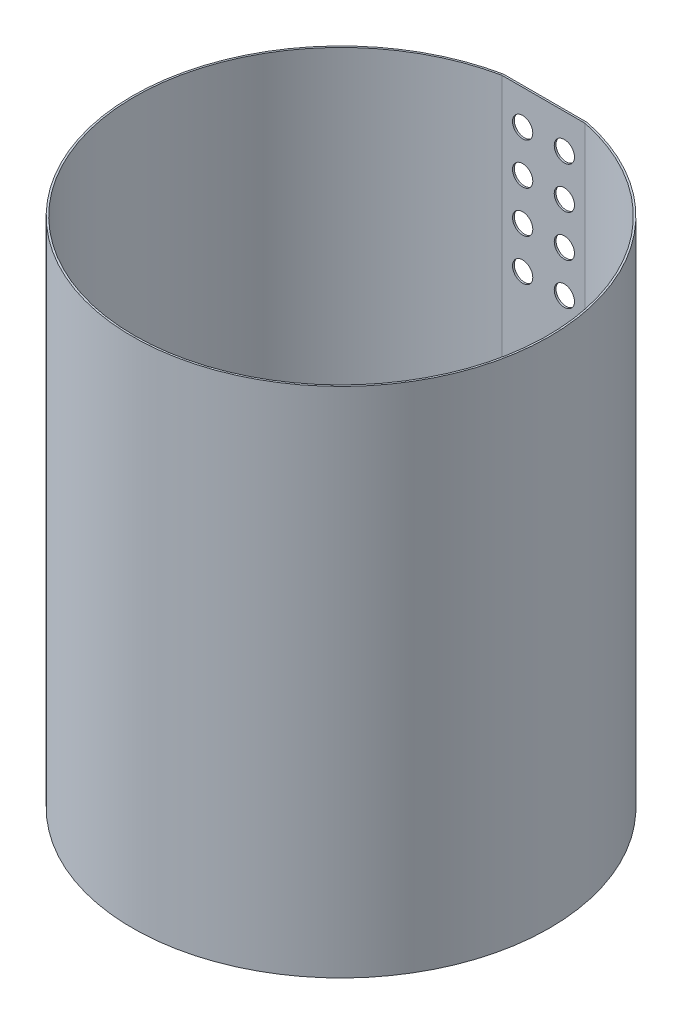
SolidWorks part; units mm, degrees
material "AISI 316 Stainless Steel Sheet (SS)"
ref_plane "Front Plane" through (0, 0, 0) normal (0, 0, 1) x (1, 0, 0)
ref_plane "Top Plane" through (0, 0, 0) normal (0, 1, 0) x (1, 0, 0)
ref_plane "Right Plane" through (0, 0, 0) normal (1, 0, 0) x (0, 0, -1)
sketch "Sketch1" plane through (0, 0, 0) normal (0, 1, 0) x (1, 0, 0)
  line L0 (-35, 169.9331) -> (35, 169.9331)
  line L1 (0, 169.9331) -> (0, 0) construction
  line L8 (-155, 37.5278) -> (-110, 115.4701)
  line L9 (-110, 115.4701) -> (-58.5, 90)
  line L10 (-58.5, 90) -> (58.5, 90)
  line L17 (-132.5, 76.4989) -> (0, 0) construction
  line L18 (110, 115.4701) -> (58.5, 90)
  line L19 (155, 37.5278) -> (110, 115.4701)
  line L20 (-155, 37.5278) -> (-107.1923, 5.6625)
  line L21 (-107.1923, 5.6625) -> (-48.6923, -95.6625)
  line L22 (-35.1525, 171.4331) -> (35.1525, 171.4331)
  circle A0 centre (0, 0) radius 170 construction
  arc A2 (-35, 169.9331) -> (35, 169.9331) centre (0, 0) ccw
  arc A39 (-35.1525, 171.4331) -> (35.1525, 171.4331) centre (0, 0) ccw
  point P7 (0, 0)
  point P12 (0, 0)
  point P13 (0, 0)
  point P14 (0, 0)
  point P15 (0, 0)
  point P16 (0, 0)
  point P17 (30, 193.6783)
  point P18 (0, 194.9585)
  point P19 (0, 0)
  point P20 (0, 0)
  point P21 (0, 0)
  point P22 (0, -3.0358)
  point P53 (-155, 76.4628)
  point P55 (-125.85, 102.5566)
  point P56 (-133.2274, 65.7183)
  point P58 (0, 90)
  dimension "D1" = 340
  dimension "D2" = 155
  dimension "D8" = 3.5
  dimension "D3" = 90
  dimension "D4" = 60
  dimension "D5" = 90
  dimension "D6" = 58.5
  dimension "D7" = 70
  dimension "D9" = 1.5
extrude "Boss-Extrude1" add sketch "Sketch1" along normal blind 430 contours L22 A39 A2 L0
sketch "Sketch4" plane through (0, 0, -171.4331) normal (0, 0, -1) x (-1, 0, 0)
  line L0 (-191, 426) -> (191, 426) construction
  line L1 (-17.5, 401) -> (0, 401) construction
  line L3 (0, 401) -> (0, 430) construction
  line L4 (35.1525, 430) -> (-35.1525, 430) construction
  line L5 (-17.5, 401) -> (17.5, 401) construction
  circle A0 centre (-17.5, 401) radius 8.5
  circle A1 centre (-17.5, 401) radius 12.5 construction
  circle A2 centre (17.5, 401) radius 12.5 construction
  circle A3 centre (17.5, 401) radius 8.5
  dimension "D1" = 17
  dimension "D2" = 25
  dimension "D3" = 25
  dimension "D4" = 35
extrude "Cut-Extrude2" cut sketch "Sketch4" against normal blind 1.5
pattern_linear "LPattern1" count 4 spacing 35 along (0, -1, 0) of "Cut-Extrude2"
